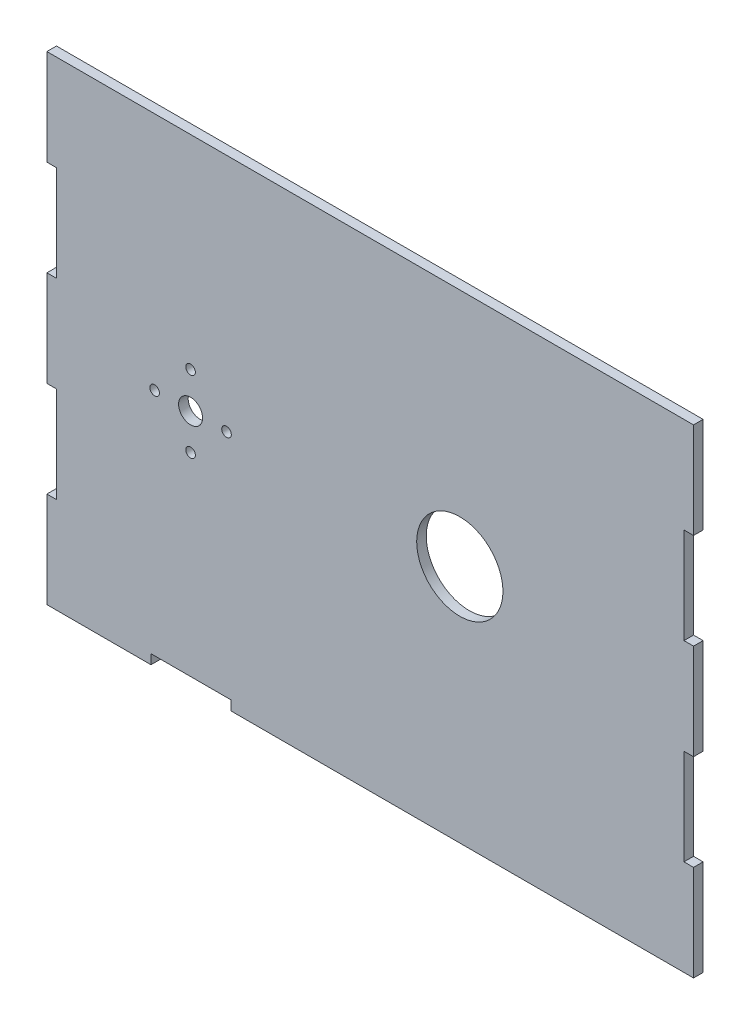
SolidWorks part; units mm, degrees
ref_plane "Front Plane" through (0, 0, 0) normal (0, 0, 1) x (1, 0, 0)
ref_plane "Top Plane" through (0, 0, 0) normal (0, 1, 0) x (1, 0, 0)
ref_plane "Right Plane" through (0, 0, 0) normal (1, 0, 0) x (0, 0, -1)
sketch "Sketch3" plane through (0, 0, 0) normal (0, 0, 1) x (1, 0, 0)
  line L1 (0, 0) -> (171.45, 0)
  line L2 (0, 0) -> (0, 127)
  line L3 (0, 127) -> (171.45, 127)
  line L4 (171.45, 0) -> (171.45, 127)
  dimension "D1" = 171.45
  dimension "D2" = 127
extrude "Boss-Extrude1" add sketch "Sketch3" along normal blind 2.54
sketch "Sketch4" plane through (0, 0, 2.54) normal (0, 0, 1) x (1, 0, 0)
  line L0 (0, 127) -> (0, 0) construction
  line L1 (0, 101.6) -> (2.54, 101.6)
  line L2 (0, 101.6) -> (0, 76.2)
  line L3 (0, 76.2) -> (2.54, 76.2)
  line L4 (2.54, 101.6) -> (2.54, 76.2)
  line L5 (171.45, 127) -> (0, 127) construction
  dimension "D1" = 25.4
  dimension "D2" = 25.4
  dimension "D3" = 2.54
extrude "Cut-Extrude1" cut sketch "Sketch4" against normal through all
pattern_linear "LPattern1" count 2 spacing 50.8 along (0, -1, 0) of "Cut-Extrude1"
sketch "Sketch6" plane through (0, 0, 2.54) normal (0, 0, 1) x (1, 0, 0)
  line L0 (171.45, 0) -> (171.45, 127) construction
  line L1 (171.45, 101.6) -> (168.91, 101.6)
  line L2 (171.45, 101.6) -> (171.45, 76.2)
  line L3 (171.45, 76.2) -> (168.91, 76.2)
  line L4 (168.91, 101.6) -> (168.91, 76.2)
  line L5 (171.45, 127) -> (0, 127) construction
  dimension "D2" = 25.4
  dimension "D1" = 2.54
  dimension "D3" = 25.4
extrude "Cut-Extrude2" cut sketch "Sketch6" against normal through all
sketch "Sketch7" plane through (0, 0, 2.54) normal (0, 0, 1) x (1, 0, 0)
  line L0 (171.45, 0) -> (171.45, 76.2) construction
  line L1 (171.45, 25.4) -> (168.91, 25.4)
  line L2 (171.45, 25.4) -> (171.45, 50.8)
  line L3 (171.45, 50.8) -> (168.91, 50.8)
  line L4 (168.91, 25.4) -> (168.91, 50.8)
  line L5 (168.91, 76.2) -> (171.45, 76.2) construction
  point P8 (170.18, 76.2)
  dimension "D2" = 25.4
  dimension "D1" = 2.54
  dimension "D3" = 25.4
extrude "Cut-Extrude3" cut sketch "Sketch7" against normal through all
sketch "Sketch8" plane through (0, 0, 0) normal (0, 0, -1) x (-1, 0, 0)
  line L0 (0, 0) -> (-171.45, 0) construction
  line L1 (-48.768, 0) -> (-27.6013, 0)
  line L2 (-48.768, 0) -> (-48.768, 2.54)
  line L3 (-48.768, 2.54) -> (-27.6013, 2.54)
  line L4 (-27.6013, 0) -> (-27.6013, 2.54)
  line L5 (-171.45, 0) -> (-171.45, 25.4) construction
  dimension "D1" = 122.682
  dimension "D2" = 2.54
  dimension "D3" = 21.1667
extrude "Cut-Extrude4" cut sketch "Sketch8" against normal through all
sketch "Sketch9" plane through (0, 0, 0) normal (0, 0, -1) x (-1, 0, 0)
  line L0 (-171.45, 127) -> (0, 127) construction
  line L1 (-171.45, 50.8) -> (-171.45, 76.2) construction
  circle A0 centre (-109.474, 63.5) radius 11.43
  dimension "D1" = 22.86
  dimension "D2" = 63.5
  dimension "D3" = 61.976
extrude "Cut-Extrude5" cut sketch "Sketch9" against normal through all
sketch "Sketch10" plane through (0, 0, 0) normal (0, 0, -1) x (-1, 0, 0)
  line L0 (-171.45, 50.8) -> (-171.45, 76.2) construction
  circle A0 centre (-38.1, 63.5) radius 3.175
  dimension "D1" = 6.35
  dimension "D2" = 133.35
extrude "Cut-Extrude6" cut sketch "Sketch10" against normal through all
sketch "Sketch11" plane through (0, 0, 0) normal (0, 0, -1) x (-1, 0, 0)
  circle A0 centre (-38.1, 73.025) radius 1.27
  circle A1 centre (-38.1, 63.5) radius 3.175 construction
  dimension "D1" = 2.54
  dimension "D2" = 9.525
extrude "Cut-Extrude8" cut sketch "Sketch11" against normal through all contours A0
sketch "Sketch14" plane through (0, 0, 0) normal (0, 0, -1) x (-1, 0, 0)
  circle A0 centre (-38.1, 63.5) radius 9.525
  dimension "D1" = 19.05
pattern_circular "CirPattern1" count 4 over 360 about axis through (38.1, 63.5, 0) along (0, 0, 1) of "Cut-Extrude8"
equation "\"D3@Sketch4\"=\"Matterial_Thickness\""
equation "\"D1@Sketch6\"=\"Matterial_Thickness\""
equation "\"D1@Sketch7\"=\"Matterial_Thickness\""
equation "\"D1@Boss-Extrude1\"=\"Matterial_Thickness\""
equation "\"Matterial_Thickness\"= \"GMaterial\""
equation "\"D2@Sketch8\"=\"Matterial_Thickness\""
equation "\"GMaterial\"= \"Foamcore\""
equation "\"MDF\" = 0.3in"
equation "\"Foamcore\"= 0.1in"
